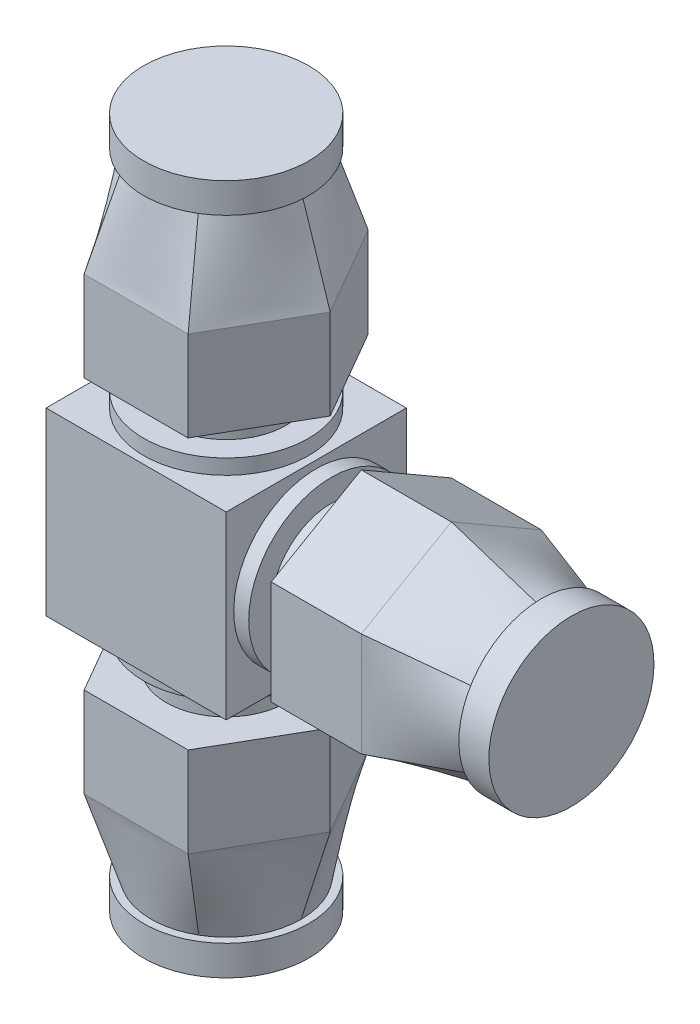
SolidWorks part; units mm, degrees
material "7075-T6 (SN)"
ref_plane "Płaszczyzna XY" through (0, 0, 0) normal (0, 0, 1) x (1, 0, 0)
ref_plane "Płaszczyzna XZ" through (0, 0, 0) normal (0, 1, 0) x (1, 0, 0)
ref_plane "Płaszczyzna YZ" through (0, 0, 0) normal (1, 0, 0) x (0, 0, -1)
sketch "Szkic1" plane through (0, 0, 0) normal (0, 0, 1) x (1, 0, 0)
  line L1 (0, -6) -> (12, -6)
  line L2 (0, -6) -> (0, 6)
  line L3 (0, 6) -> (12, 6)
  line L4 (12, -6) -> (12, 6)
  dimension "D1" = 12
extrude "Dodanie-wyciągnięcie1" add sketch "Szkic1" along normal blind 12
sketch "Szkic2" plane through (0, -6, 0) normal (0, -1, 0) x (1, 0, 0)
  line L0 (0, 12) -> (12, 12) construction
  line L1 (12, 12) -> (12, 0) construction
  circle A0 centre (6, 6) radius 5.5
  point P2 (6, 12)
  point P3 (12, 6)
  dimension "D1" = 11
extrude "Dodanie-wyciągnięcie2" add sketch "Szkic2" along normal blind 1 contours A0
sketch "Szkic3" plane through (0, -7, 0) normal (0, -1, 0) x (1, 0, 0)
  circle A0 centre (6, 6) radius 4
  circle A1 centre (6, 6) radius 5.5 construction
  dimension "D1" = 8
extrude "Dodanie-wyciągnięcie3" add sketch "Szkic3" along normal blind 2
sketch "Szkic4" plane through (0, -9, 0) normal (0, -1, 0) x (1, 0, 0)
  line L1 (9.4641, 12) -> (2.5359, 12)
  line L2 (2.5359, 12) -> (-0.9282, 6)
  line L3 (-0.9282, 6) -> (2.5359, 0)
  line L4 (2.5359, 0) -> (9.4641, 0)
  line L5 (9.4641, 0) -> (12.9282, 6)
  line L6 (12.9282, 6) -> (9.4641, 12)
  circle A0 centre (6, 6) radius 6 construction
  circle A1 centre (6, 6) radius 4 construction
  circle A2 centre (6, 6) radius 4
  circle M3 centre (6, 6) radius 4
  dimension "D1" = 12
extrude "Dodanie-wyciągnięcie4" add sketch "Szkic4" along normal blind 6 contours M3 | L5 L6 L1 L2 L3 L4 M3
ref_plane "Płaszczyzna1" through (0, -21, 0) normal (0, -1, 0) x (-1, 0, 0)
sketch "Szkic5" plane through (0, -21, 0) normal (0, -1, 0) x (-1, 0, 0)
  circle A0 centre (-6, -6) radius 5.5 construction
  circle A1 centre (-6, -6) radius 5.5 construction
  circle A2 centre (-6, -6) radius 5
  dimension "D1" = 10
sketch "Szkic6" plane through (0, -15, 0) normal (0, -1, 0) x (1, 0, 0)
  line L6 (9.4641, 0) -> (12.9282, 6)
  line L7 (12.9282, 6) -> (9.4641, 12)
  line L8 (9.4641, 12) -> (2.5359, 12)
  line L9 (2.5359, 12) -> (-0.9282, 6)
  line L10 (-0.9282, 6) -> (2.5359, 0)
  line L11 (2.5359, 0) -> (9.4641, 0)
  line L12 (9.4641, 0) -> (12.9282, 6)
  line L13 (12.9282, 6) -> (9.4641, 12)
  line L14 (9.4641, 12) -> (2.5359, 12)
  line L15 (2.5359, 12) -> (-0.9282, 6)
  line L16 (-0.9282, 6) -> (2.5359, 0)
  line L17 (2.5359, 0) -> (9.4641, 0)
  dimension "D1" = 0
loft "Wyciągnięcie po profilach1" add profiles "Szkic5", "Szkic6"
sketch "Szkic7" plane through (0, -21, 0) normal (0, -1, 0) x (1, 0, 0)
  circle A0 centre (6, 6) radius 5.5
  arc A6 (8.5, 1.6699) -> (11, 6) centre (6, 6) ccw
  arc A7 (11, 6) -> (8.5, 10.3301) centre (6, 6) ccw
  arc A8 (8.5, 10.3301) -> (3.5, 10.3301) centre (6, 6) ccw
  arc A9 (3.5, 10.3301) -> (1, 6) centre (6, 6) ccw
  arc A10 (1, 6) -> (3.5, 1.6699) centre (6, 6) ccw
  arc A11 (3.5, 1.6699) -> (8.5, 1.6699) centre (6, 6) ccw
  arc A12 (8.5, 1.6699) -> (11, 6) centre (6, 6) ccw
  arc A13 (11, 6) -> (8.5, 10.3301) centre (6, 6) ccw
  arc A14 (8.5, 10.3301) -> (3.5, 10.3301) centre (6, 6) ccw
  arc A15 (3.5, 10.3301) -> (1, 6) centre (6, 6) ccw
  arc A16 (1, 6) -> (3.5, 1.6699) centre (6, 6) ccw
  arc A17 (3.5, 1.6699) -> (8.5, 1.6699) centre (6, 6) ccw
  dimension "D2" = 11
  dimension "D1" = 0
extrude "Dodanie-wyciągnięcie5" add sketch "Szkic7" along normal blind 2
mirror "Lustro1" about plane through (0, 0, 0) normal (0, 1, 0) of "Dodanie-wyciągnięcie5", "Wyciągnięcie po profilach1", "Dodanie-wyciągnięcie4", "Dodanie-wyciągnięcie3", "Dodanie-wyciągnięcie2"
sketch "Szkic8" plane through (12, 0, 0) normal (1, 0, 0) x (0, 0, -1)
  line L0 (-12, 6) -> (0, 6) construction
  circle A0 centre (-6, 0) radius 5.5
  point P2 (-6, 6)
  dimension "D1" = 11
extrude "Dodanie-wyciągnięcie6" add sketch "Szkic8" along normal blind 1
sketch "Szkic9" plane through (13, 0, 0) normal (1, 0, 0) x (0, 0, -1)
  circle A0 centre (-6, 0) radius 4
  circle A1 centre (-6, 0) radius 5.5
  circle A2 centre (-6, 0) radius 5.5
  dimension "D2" = 8
  dimension "D1" = 0
extrude "Dodanie-wyciągnięcie7" add sketch "Szkic9" along normal blind 2 contours A0
sketch "Szkic10" plane through (15, 0, 0) normal (1, 0, 0) x (0, 0, -1)
  line L1 (-6, 6.9282) -> (-12, 3.4641)
  line L2 (-12, 3.4641) -> (-12, -3.4641)
  line L3 (-12, -3.4641) -> (-6, -6.9282)
  line L4 (-6, -6.9282) -> (0, -3.4641)
  line L5 (0, -3.4641) -> (0, 3.4641)
  line L6 (0, 3.4641) -> (-6, 6.9282)
  circle A0 centre (-6, 0) radius 6 construction
  dimension "D1" = 12
extrude "Dodanie-wyciągnięcie8" add sketch "Szkic10" along normal blind 6
ref_plane "Płaszczyzna2" through (27, 0, 0) normal (1, 0, 0) x (0, 0, -1)
sketch "Szkic11" plane through (27, 0, 0) normal (1, 0, 0) x (0, 0, -1)
  circle A0 centre (-6, 0) radius 5
  circle A1 centre (-6, 0) radius 5.5
  circle A2 centre (-6, 0) radius 5.5 construction
  dimension "D2" = 10
  dimension "D1" = 0
sketch "Szkic12" plane through (21, 0, 0) normal (1, 0, 0) x (0, 0, -1)
  line L6 (0, 3.4641) -> (-6, 6.9282)
  line L7 (-6, 6.9282) -> (-12, 3.4641)
  line L8 (-12, 3.4641) -> (-12, -3.4641)
  line L9 (-12, -3.4641) -> (-6, -6.9282)
  line L10 (-6, -6.9282) -> (0, -3.4641)
  line L11 (0, -3.4641) -> (0, 3.4641)
  line L12 (0, 3.4641) -> (-6, 6.9282)
  line L13 (-6, 6.9282) -> (-12, 3.4641)
  line L14 (-12, 3.4641) -> (-12, -3.4641)
  line L15 (-12, -3.4641) -> (-6, -6.9282)
  line L16 (-6, -6.9282) -> (0, -3.4641)
  line L17 (0, -3.4641) -> (0, 3.4641)
  dimension "D1" = 0
loft "Wyciągnięcie po profilach2" add profiles "Szkic12", "Szkic11"
sketch "Szkic13" plane through (27, 0, 0) normal (1, 0, 0) x (0, 0, -1)
  circle A0 centre (-6, 0) radius 5.5
  arc A1 (-1.6699, -2.5) -> (-1.6699, 2.5) centre (-6, 0) ccw construction
  dimension "D1" = 11
extrude "Dodanie-wyciągnięcie9" add sketch "Szkic13" along normal blind 2
